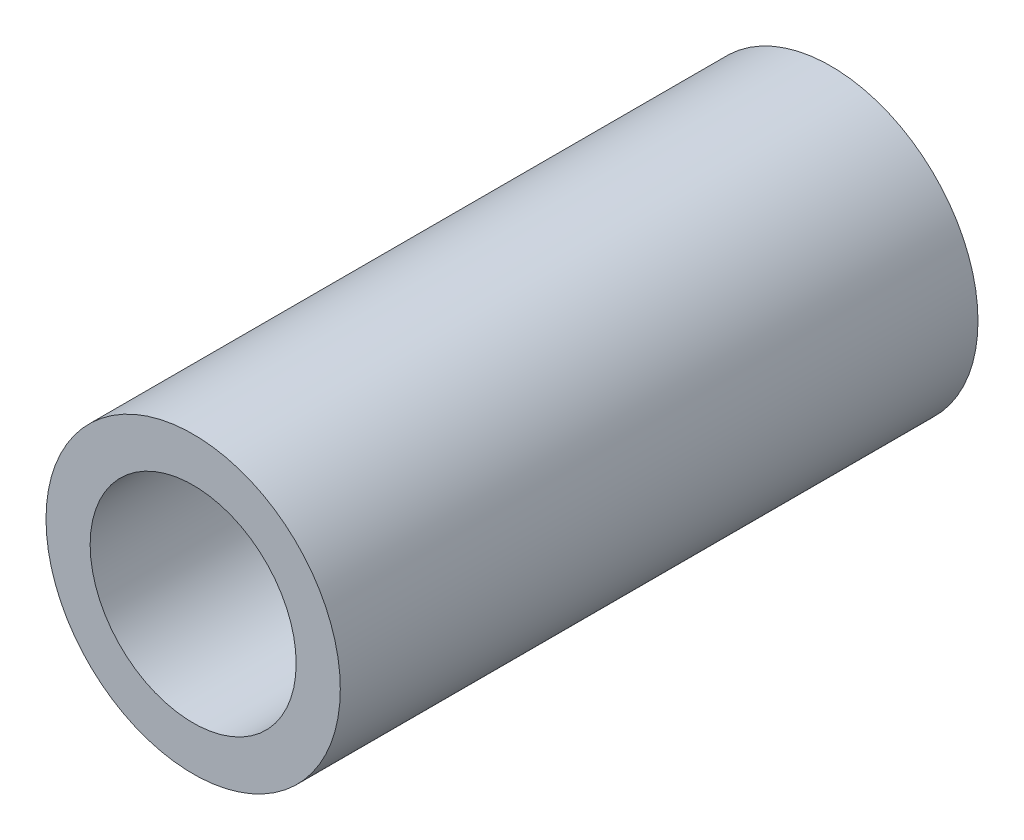
SolidWorks part; units mm, degrees
ref_plane "Plano frontal" through (0, 0, 0) normal (0, 0, 1) x (1, 0, 0)
ref_plane "Plano superior" through (0, 0, 0) normal (0, 1, 0) x (1, 0, 0)
ref_plane "Plano direito" through (0, 0, 0) normal (1, 0, 0) x (0, 0, -1)
sketch "Esboço1" plane through (0, 0, 0) normal (0, 0, 1) x (1, 0, 0)
  circle A0 centre (0, 0) radius 3
  circle A1 centre (0, 0) radius 2.1
  dimension "D1" = 6
  dimension "D2" = 4.2
extrude "Ressalto-extrusão1" add sketch "Esboço1" along normal blind 13
